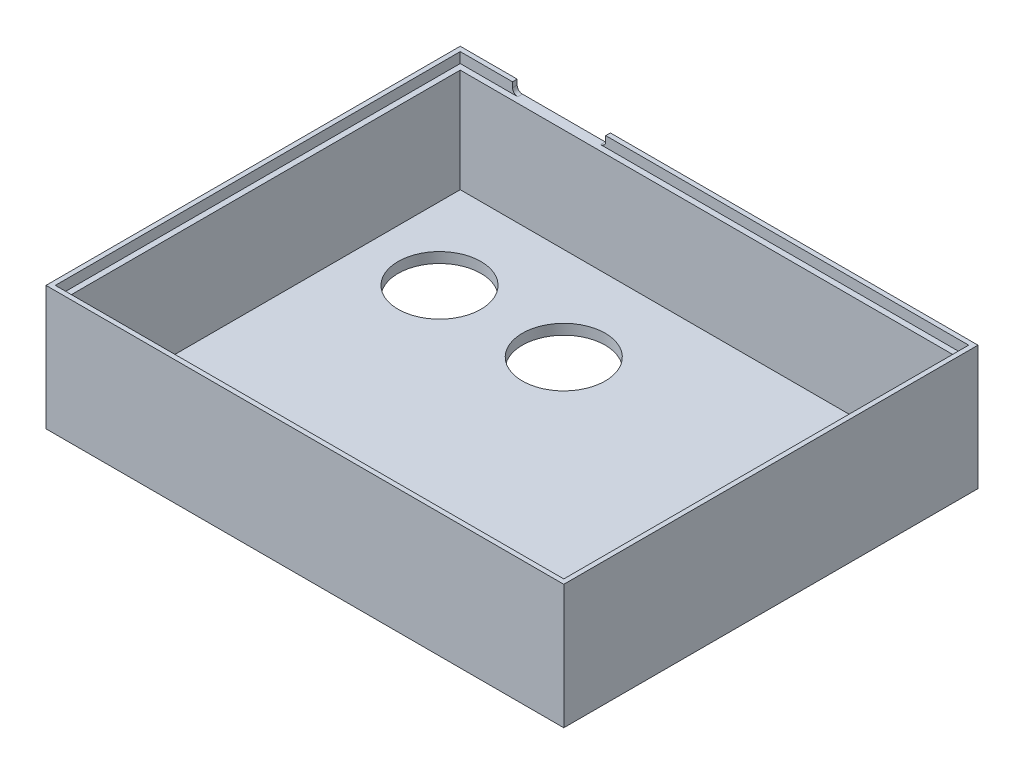
SolidWorks part; units mm, degrees
ref_plane "Plan de face" through (0, 0, 0) normal (0, 0, 1) x (1, 0, 0)
ref_plane "Plan de dessus" through (0, 0, 0) normal (0, 1, 0) x (1, 0, 0)
ref_plane "Plan de droite" through (0, 0, 0) normal (1, 0, 0) x (0, 0, -1)
sketch "Esquisse1" plane through (0, 0, 0) normal (0, 1, 0) x (1, 0, 0)
  line L1 (50, 40) -> (-50, 40)
  line L2 (50, 40) -> (50, -40)
  line L3 (50, -40) -> (-50, -40)
  line L4 (-50, 40) -> (-50, -40)
  line L5 (50, 40) -> (-50, -40) construction
  line L6 (50, -40) -> (-50, 40) construction
  point P0 (0, 0)
  dimension "D1" = 100
  dimension "D2" = 80
extrude "Boss.-Extru.1" add sketch "Esquisse1" along normal blind 2
sketch "Esquisse2" plane through (0, 2, 0) normal (0, 1, 0) x (1, 0, 0)
  line L0 (-48, 38) -> (-48, -38)
  line L1 (-48, -38) -> (48, -38)
  line L2 (48, -38) -> (48, 38)
  line L3 (48, 38) -> (-48, 38)
  line L4 (-50, 40) -> (-50, -40)
  line L5 (-50, -40) -> (50, -40)
  line L6 (50, -40) -> (50, 40)
  line L7 (50, 40) -> (-50, 40)
  line L8 (-50, 40) -> (-50, -40)
  line L9 (-50, -40) -> (50, -40)
  line L10 (50, -40) -> (50, 40)
  line L11 (50, 40) -> (-50, 40)
  dimension "D1" = 0
  dimension "D2" = 2
extrude "Boss.-Extru.2" add sketch "Esquisse2" along normal blind 20
sketch "Esquisse5" plane through (0, 22, 0) normal (0, 1, 0) x (1, 0, 0)
  line L8 (49.1, -39.1) -> (49.1, 39.1)
  line L9 (-49.1, -39.1) -> (49.1, -39.1)
  line L10 (-49.1, 39.1) -> (-49.1, -39.1)
  line L11 (49.1, 39.1) -> (-49.1, 39.1)
  line L12 (49.1, -39.1) -> (49.1, 39.1)
  line L13 (-49.1, -39.1) -> (49.1, -39.1)
  line L14 (-49.1, 39.1) -> (-49.1, -39.1)
  line L15 (49.1, 39.1) -> (-49.1, 39.1)
  line L16 (50, -40) -> (50, 40) construction
  line L17 (-50, -40) -> (50, -40) construction
  line L18 (-50, 40) -> (-50, -40) construction
  line L19 (50, 40) -> (-50, 40) construction
  line L20 (50, -40) -> (50, 40)
  line L21 (-50, -40) -> (50, -40)
  line L22 (-50, 40) -> (-50, -40)
  line L23 (50, 40) -> (-50, 40)
  dimension "D1" = 1.1
extrude "Boss.-Extru.3" add sketch "Esquisse5" along normal blind 2
sketch "Esquisse6" plane through (0, 0, -40) normal (0, 0, -1) x (-1, 0, 0)
  line L0 (21, 24) -> (21, 22)
  line L1 (50.1, 24) -> (-49.9, 24) construction
  line L3 (21, 22) -> (39, 22)
  line L4 (39, 22) -> (39, 24)
  line L5 (39, 24) -> (21, 24)
  line L6 (50, 24) -> (50, 0) construction
  dimension "D1" = 18
  dimension "D2" = 11
  dimension "D3" = 2
extrude "Enlèv. mat.-Extru.3" cut sketch "Esquisse6" against normal blind 10
fillet "Congé1" radius 1 2 edges at (-21, 22, -39.55) (-39, 22, -39.55)
sketch "Esquisse7" plane through (0, 0, 0) normal (0, -1, 0) x (1, 0, 0)
  line L0 (-34, -20) -> (-10, -20) construction
  line L2 (50, -40) -> (-50, -40) construction
  line L3 (-50, -40) -> (-50, 40) construction
  circle A0 centre (-34, -20) radius 8
  circle A1 centre (-10, -20) radius 8
  dimension "D2" = 16
  dimension "D3" = 16
  dimension "D1" = 20
  dimension "D4" = 24
  dimension "D5" = 16
extrude "Enlèv. mat.-Extru.4" cut sketch "Esquisse7" against normal blind 10
